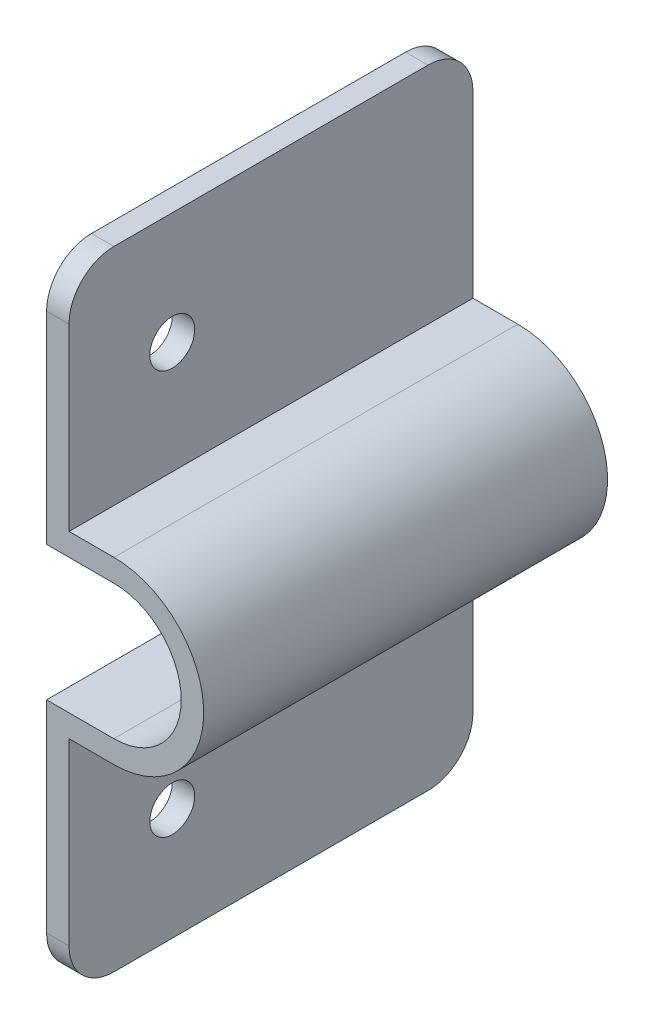
SolidWorks part; units mm, degrees
material "6061-T6 (SS)"
ref_plane "Front Plane" through (0, 0, 0) normal (0, 0, 1) x (1, 0, 0)
ref_plane "Top Plane" through (0, 0, 0) normal (0, 1, 0) x (1, 0, 0)
ref_plane "Right Plane" through (0, 0, 0) normal (1, 0, 0) x (0, 0, -1)
sketch "Sketch1" plane through (0, 0, 0) normal (0, 0, 1) x (1, 0, 0)
  line L0 (10.16, 323.0894) -> (10.16, 234.1894)
  line L1 (10.16, -19.9824) -> (10.16, 1018.8869) construction
  line L2 (10.16, 278.6394) -> (19.685, 278.6394) construction
  line L3 (10.16, 234.1894) -> (13.335, 234.1894)
  line L4 (10.16, 234.1894) -> (10.16, 323.0894)
  line L5 (10.16, 323.0894) -> (13.335, 323.0894)
  line L6 (13.335, 234.1894) -> (13.335, 323.0894)
  line L7 (19.685, 288.1644) -> (13.335, 288.1644)
  line L8 (19.685, 269.1144) -> (13.335, 269.1144)
  line L9 (19.685, 291.3394) -> (13.335, 291.3394)
  line L10 (19.685, 265.9394) -> (13.335, 265.9394)
  line L11 (13.335, 288.1644) -> (10.16, 288.1644)
  line L12 (13.335, 269.1144) -> (10.16, 269.1144)
  circle A0 centre (19.685, 278.6394) radius 9.525
  circle A1 centre (19.685, 278.6394) radius 12.7
  ellipse E0 centre (16.7619, 278.6394) end of major axis (26.2869, 278.6394) minor radius 9.5021 construction
  dimension "D4" = 19.05
  dimension "D5" = 3.175
  dimension "D1" = 88.9
  dimension "D2" = 44.45
  dimension "D3" = 3.175
extrude "Boss-Extrude1" add sketch "Sketch1" against normal blind 88.9 contours L11 L6 L5 L0 | A1 L9 L6 L7 | A1 L7 A0 L8 | A1 L8 L6 L10 | L6 L12 L0 L3 | L6 A1 L11 | L12 A1 L6
sketch "Sketch2" plane through (13.335, 0, 0) normal (1, 0, 0) x (0, 0, -1)
  line L0 (88.9, 307.2144) -> (0, 307.2144) construction
  line L1 (88.9, 291.3394) -> (88.9, 323.0894) construction
  line L2 (0, 291.3394) -> (0, 323.0894) construction
  line L3 (0, 250.0644) -> (88.9, 250.0644) construction
  line L4 (0, 234.1894) -> (0, 265.9394) construction
  line L5 (88.9, 234.1894) -> (88.9, 265.9394) construction
  circle A1 centre (46.355, 250.0644) radius 3.175
  circle A2 centre (46.355, 307.2144) radius 3.175
  dimension "D1" = 6.35
  dimension "D2" = 42.545
  dimension "D3" = 42.545
extrude "Cut-Extrude1" cut sketch "Sketch2" against normal through all
fillet "Fillet1" radius 6.35 4 edges at (11.7475, 234.1894, 0) (11.7475, 234.1894, -88.9) (11.7475, 323.0894, 0) (11.7475, 323.0894, -88.9)
sketch "Sketch3" plane through (13.335, 0, 0) normal (1, 0, 0) x (0, 0, -1)
  line L0 (82.55, 234.1894) -> (6.35, 234.1894) construction
  line L1 (88.9, 323.0894) -> (31.75, 323.0894)
  line L2 (88.9, 323.0894) -> (88.9, 234.1894)
  line L3 (88.9, 234.1894) -> (31.75, 234.1894)
  line L4 (31.75, 323.0894) -> (31.75, 234.1894)
  line L5 (88.9, 291.3394) -> (88.9, 316.7394) construction
  line L6 (82.55, 323.0894) -> (6.35, 323.0894) construction
  line L7 (0, 291.3394) -> (0, 316.7394) construction
  line L8 (31.75, 234.1894) -> (0, 234.1894)
  line L9 (31.75, 234.1894) -> (31.75, 323.0894)
  line L10 (31.75, 323.0894) -> (0, 323.0894)
  line L11 (0, 234.1894) -> (0, 323.0894)
  line M7 (0, 265.9394) -> (0, 240.5394)
  arc M8 (0, 240.5394) -> (6.35, 234.1894) centre (6.35, 240.5394) ccw
  line M9 (6.35, 234.1894) -> (82.55, 234.1894)
  line M12 (88.9, 265.9394) -> (0, 265.9394)
  dimension "D1" = 57.15
extrude "Cut-Extrude2" cut sketch "Sketch3" against normal through all and the other way through all contours L11 L4 L10 M12 | L4 M12 M7 M8 M9
fillet "Fillet2" radius 6.35 2 edges at (11.7475, 234.1894, -31.75) (11.7475, 323.0894, -31.75)
